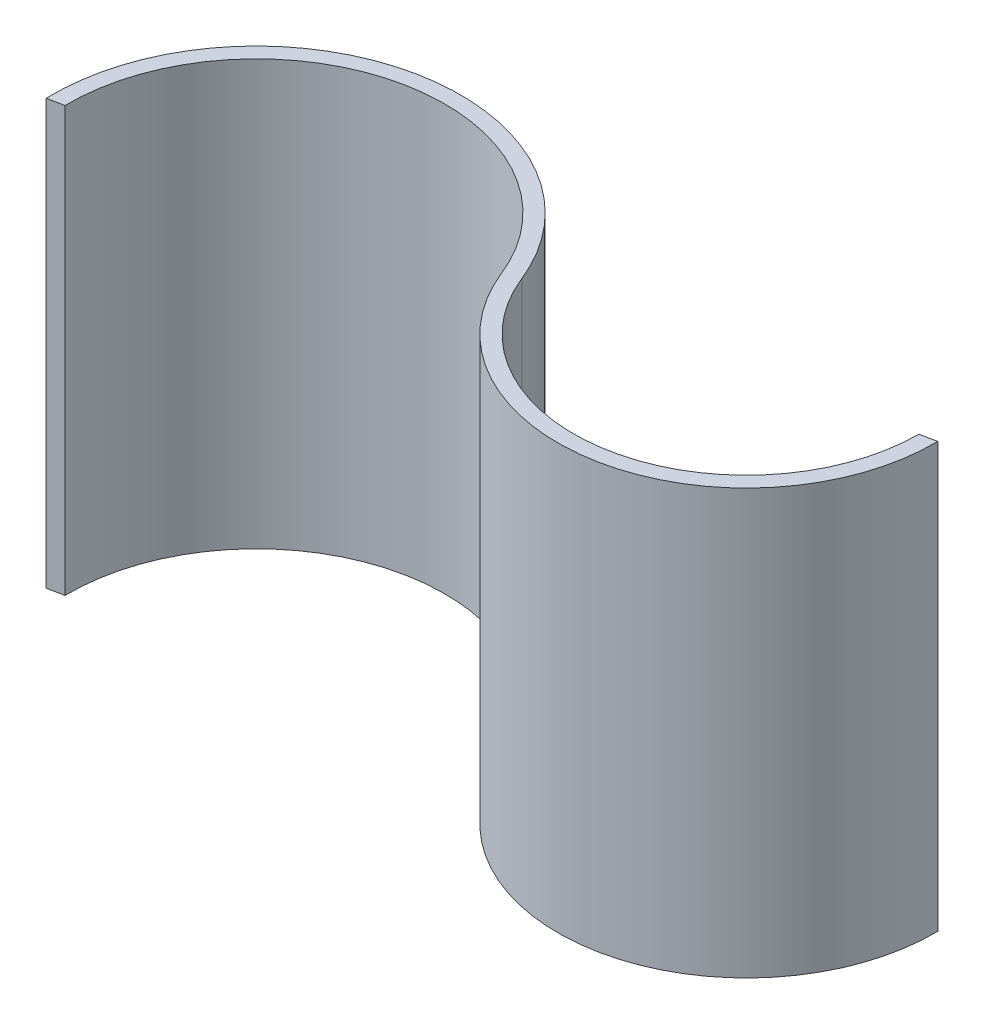
SolidWorks part; units mm, degrees
ref_plane "Спереди" through (0, 0, 0) normal (0, 0, 1) x (1, 0, 0)
ref_plane "Сверху" through (0, 0, 0) normal (0, 1, 0) x (1, 0, 0)
ref_plane "Справа" through (0, 0, 0) normal (1, 0, 0) x (0, 0, -1)
sketch "Эскиз4" plane through (0, 0, 0) normal (0, 1, 0) x (1, 0, 0)
  line L0 (0, 60) -> (0, -60) construction
  line L1 (-150, 60) -> (150, 60) construction
  line L2 (-150, 60) -> (-150, -60) construction
  line L3 (-150, -60) -> (150, -60) construction
  line L4 (150, 60) -> (150, -60) construction
  line L5 (-150, 0) -> (150, 0) construction
  line L6 (-150, -60) -> (0, 0) construction
  line L7 (0, 0) -> (150, 60) construction
  line L8 (-150, -30) -> (150, 30) construction
  line L10 (110.7084, 22.1417) -> (115.7025, 23.1405)
  line L11 (-120.6822, -24.1364) -> (-115.7025, -23.1405)
  arc A5 (0, 0) -> (115.7025, 23.1405) centre (55.7086, 22.2834) ccw
  arc A8 (4.6424, 1.857) -> (110.7084, 22.1417) centre (55.7086, 22.2834) ccw
  arc A10 (0, 0) -> (-115.7025, -23.1405) centre (-55.7086, -22.2834) ccw
  arc A12 (4.6424, 1.857) -> (-120.6822, -24.1364) centre (-55.7086, -22.2834) ccw
  point P8 (0, 0)
  point P21 (-150, -30)
  point P22 (150, 30)
  dimension "D12" = 5
  dimension "D3" = 55
  dimension "D4" = 60
  dimension "D1" = 120
  dimension "D2" = 300
  dimension "D8" = 30
  dimension "D9" = 30
extrude "Бобышка-Вытянуть1" add sketch "Эскиз4" along normal blind 135
